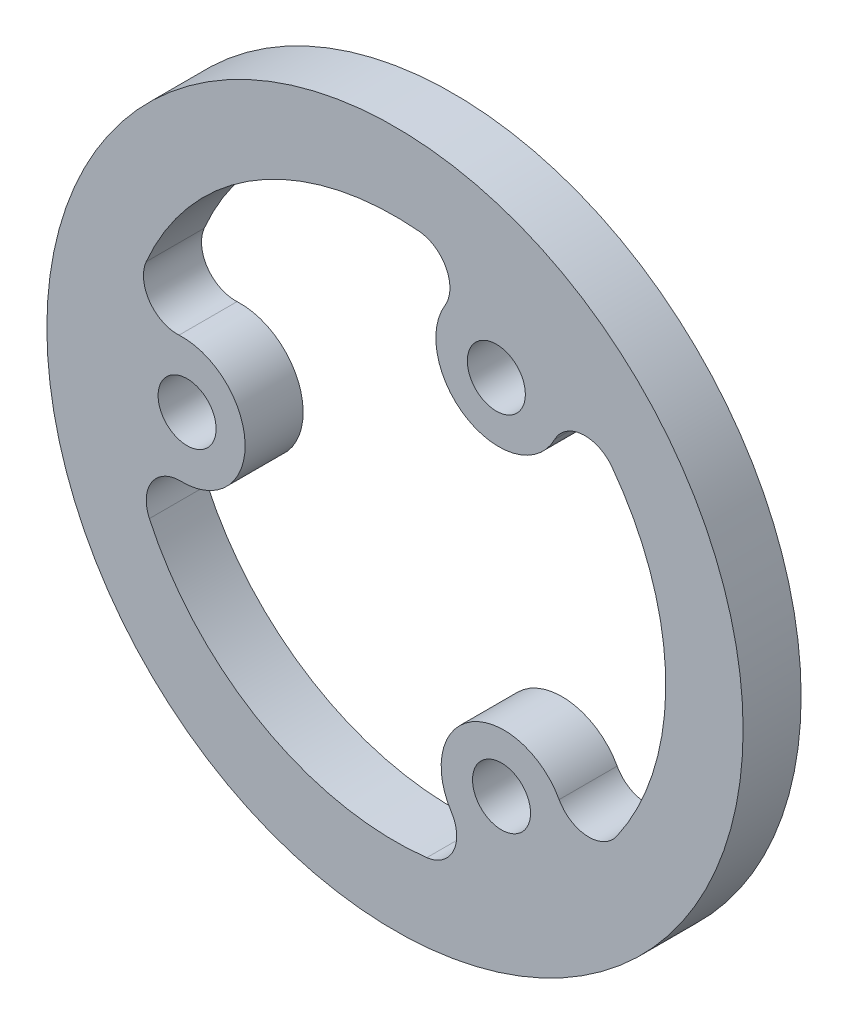
SolidWorks part; units mm, degrees
ref_plane "Plan de face" through (0, 0, 0) normal (0, 0, 1) x (1, 0, 0)
ref_plane "Plan de dessus" through (0, 0, 0) normal (0, 1, 0) x (1, 0, 0)
ref_plane "Plan de droite" through (0, 0, 0) normal (1, 0, 0) x (0, 0, -1)
sketch "Esquisse1" plane through (0, 0, 0) normal (0, 0, 1) x (1, 0, 0)
  line L0 (5.2405, 9.3862) -> (0, 0) construction
  circle A0 centre (0, 0) radius 18
  circle A9 centre (5.2405, 9.3862) radius 1.5
  circle A19 centre (0, 0) radius 7.75 construction
  circle A21 centre (0, 0) radius 9 construction
  arc A22 (11.4536, -8.0507) -> (11.2172, 8.3771) centre (0, 0) ccw
  arc A25 (8.487, -7.885) -> (11.4536, -8.0507) centre (10.0219, -7.0444) ccw
  arc A28 (2.5851, 11.2925) -> (8.2566, 8.126) centre (5.3623, 9.6045) ccw
  arc A29 (2.5851, 11.2925) -> (1.2453, 13.9445) centre (1.0897, 12.2014) ccw
  arc A30 (11.2172, 8.3771) -> (8.2566, 8.126) centre (9.815, 7.3299) ccw
  arc A31 (1.2453, 13.9445) -> (-12.8633, 5.5258) centre (0, 0) ccw
  arc A32 (-12.699, -5.8938) -> (1.6462, -13.9029) centre (0, 0) ccw
  circle A36 centre (5.5084, -9.2314) radius 1.5
  arc A37 (8.487, -7.885) -> (2.909, -11.2134) centre (5.6365, -9.4461) ccw
  arc A38 (1.6462, -13.9029) -> (2.909, -11.2134) centre (1.4404, -12.165) ccw
  arc A39 (-11.0721, -3.4075) -> (-12.699, -5.8938) centre (-11.1116, -5.157) ccw
  circle A40 centre (-10.7489, -0.1547) radius 1.5
  arc A41 (-11.0721, -3.4075) -> (-11.1656, 3.0874) centre (-10.9989, -0.1583) ccw
  arc A42 (-12.8633, 5.5258) -> (-11.1656, 3.0874) centre (-11.2554, 4.8351) ccw
  point P3 (0, 0)
  point P4 (0, 0)
  point P32 (0, 0)
  point P37 (0, 0)
  point P49 (0, 0)
  dimension "D1" = 36
  dimension "D2" = 10.7489
  dimension "D3" = 3
  dimension "D5" = 15.5
  dimension "D7" = 18
  dimension "D14" = 28
  dimension "D6" = 10.75
extrude "Boss.-Extru.1" add sketch "Esquisse1" along normal blind 3
